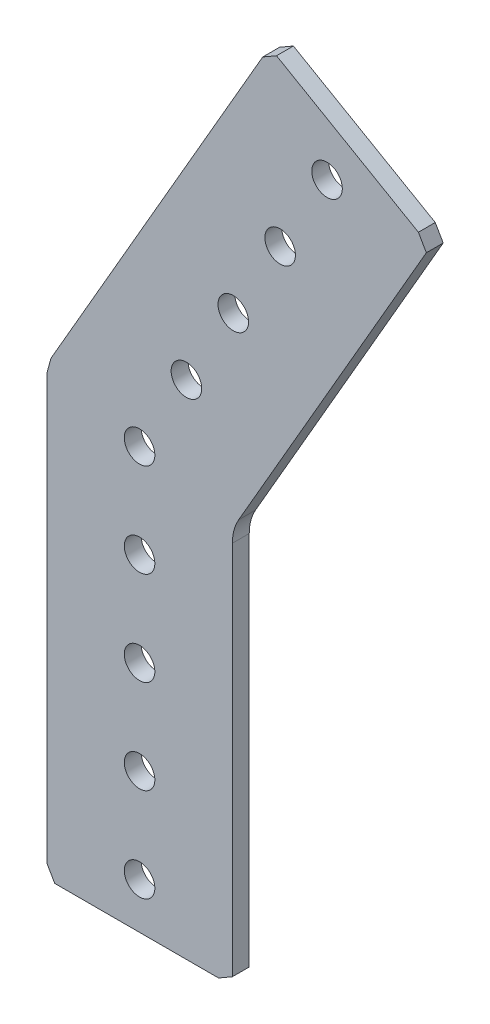
SolidWorks part; units mm, degrees
ref_plane "Front Plane" through (0, 0, 0) normal (0, 0, 1) x (1, 0, 0)
ref_plane "Top Plane" through (0, 0, 0) normal (0, 1, 0) x (1, 0, 0)
ref_plane "Right Plane" through (0, 0, 0) normal (1, 0, 0) x (0, 0, -1)
ref_plane "Plane1" through (0, 0, 2.286) normal (0, 0, 1) x (1, 0, 0)
sketch "Sketch1" plane through (0, 0, 2.286) normal (0, 0, 1) x (1, 0, 0)
  line L0 (16.6881, 54.0506) -> (-12.0142, 4.3368)
  line L1 (-12.0142, 4.3368) -> (-12.573, 2.2513)
  line L2 (-12.573, 2.2513) -> (-12.573, -55.1533)
  line L3 (-12.573, -55.1533) -> (-11.4935, -57.023)
  line L4 (-11.4935, -57.023) -> (10.7033, -57.023)
  line L5 (10.7033, -57.023) -> (12.573, -55.9435)
  line L6 (12.573, -55.9435) -> (12.573, -5.0704)
  line L7 (13.4237, -1.8954) -> (38.8603, 42.162)
  line L8 (38.8603, 42.162) -> (37.7808, 44.0317)
  line L9 (37.7808, 44.0317) -> (18.5578, 55.1301)
  line L10 (18.5578, 55.1301) -> (16.6881, 54.0506)
  arc A0 (12.573, -5.0704) -> (13.4237, -1.8954) centre (18.923, -5.0704) cw
  circle A1 centre (0, 0) radius 2.0701
  circle A2 centre (0, -38.1) radius 2.0701
  circle A3 centre (0, -12.7) radius 2.0701
  circle A4 centre (0, -25.4) radius 2.0701
  circle A5 centre (0, -50.8) radius 2.0701
  circle A6 centre (19.05, 32.9956) radius 2.0701
  circle A7 centre (6.35, 10.9985) radius 2.0701
  circle A8 centre (12.7, 21.997) radius 2.0701
  circle A9 centre (25.4, 43.9941) radius 2.0701
extrude "Boss-Extrude1" add sketch "Sketch1" against normal blind 2.286
